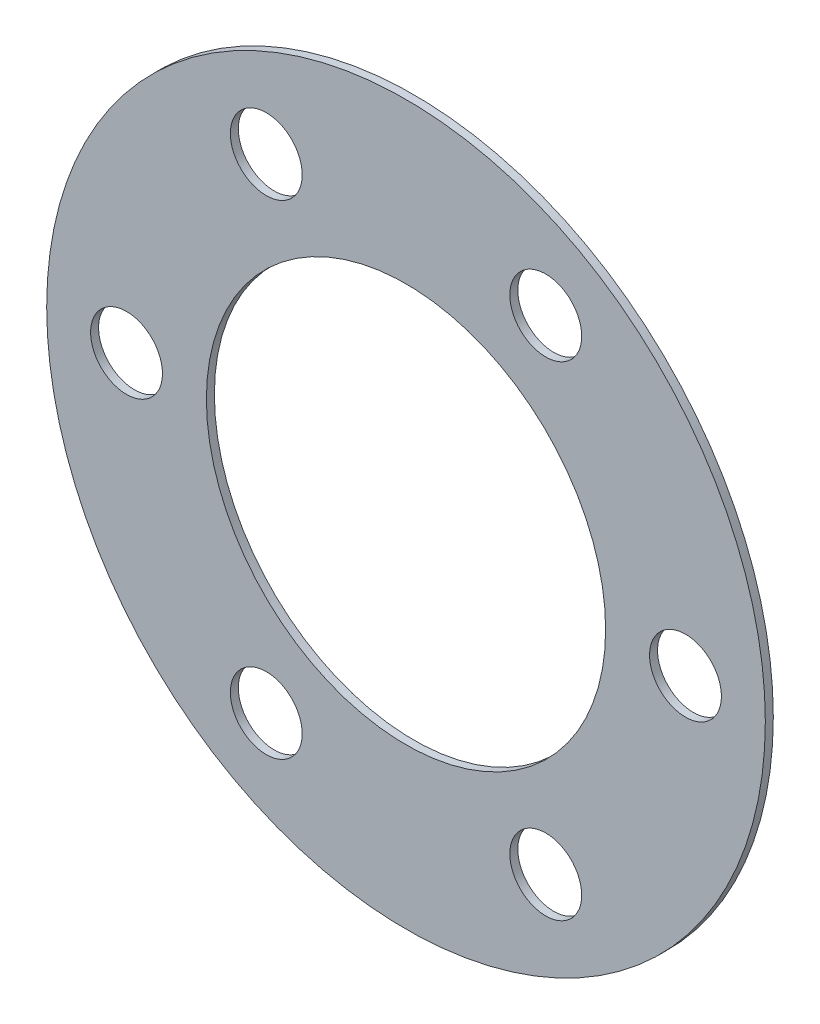
SolidWorks part; units mm, degrees
ref_plane "Přední rovina" through (0, 0, 0) normal (0, 0, 1) x (1, 0, 0)
ref_plane "Vrchní rovina" through (0, 0, 0) normal (0, 1, 0) x (1, 0, 0)
ref_plane "Pravá rovina" through (0, 0, 0) normal (1, 0, 0) x (0, 0, -1)
sketch "Skica2" plane through (0, 0, 0) normal (0, 0, 1) x (1, 0, 0)
  circle A0 centre (0, 0) radius 35 construction
  circle A1 centre (0, 0) radius 25
  circle A3 centre (0, 0) radius 45 construction
  circle A4 centre (17.5, 30.3109) radius 4.5 construction
  circle A5 centre (35, 0) radius 4.5 construction
  circle A6 centre (17.5, -30.3109) radius 4.5 construction
  circle A7 centre (-17.5, -30.3109) radius 4.5 construction
  circle A8 centre (-35, 0) radius 4.5 construction
  circle A9 centre (-17.5, 30.3109) radius 4.5 construction
  circle A10 centre (0, 0) radius 45
  circle A11 centre (17.5, 30.3109) radius 4.5
  circle A12 centre (35, 0) radius 4.5
  circle A13 centre (17.5, -30.3109) radius 4.5
  circle A14 centre (-17.5, -30.3109) radius 4.5
  circle A15 centre (-35, 0) radius 4.5
  circle A16 centre (-17.5, 30.3109) radius 4.5
  dimension "D1" = 50
extrude "Přidat vysunutím1" add sketch "Skica2" along normal blind 1
